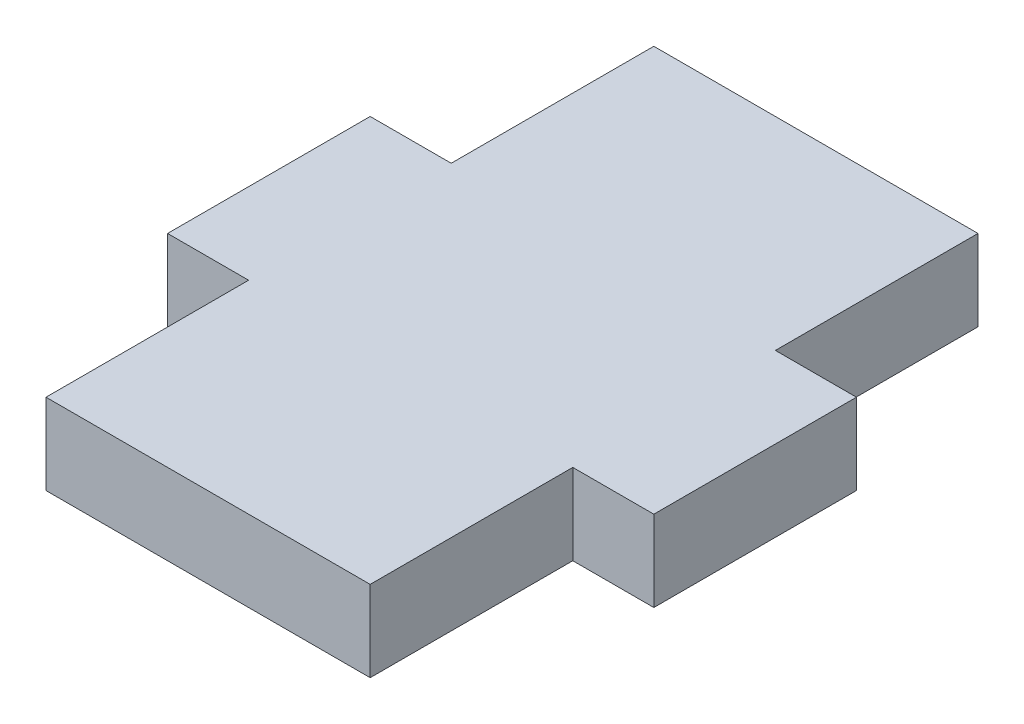
SolidWorks part; units mm, degrees
material "Stal węglowa"
ref_plane "Płaszczyzna przednia" through (0, 0, 0) normal (0, 0, 1) x (1, 0, 0)
ref_plane "Płaszczyzna górna" through (0, 0, 0) normal (0, 1, 0) x (1, 0, 0)
ref_plane "Płaszczyzna prawa" through (0, 0, 0) normal (1, 0, 0) x (0, 0, -1)
sketch "Szkic1" plane through (0, 0, 0) normal (0, 0, 1) x (1, 0, 0)
  line L0 (-8, -373.3248) -> (-8, -375.3201)
  line L1 (0, -373.3248) -> (0, -375.3201)
  line L3 (-8, -375.3201) -> (0, -375.3201)
  line L8 (-8, -373.3248) -> (-8, -360.3201)
  line L9 (-8, -360.3201) -> (-10, -360.3201)
  line L10 (-10, -360.3201) -> (-10, -375.3201)
  line L11 (-10, -375.3201) -> (2, -375.3201)
  line L12 (2, -375.3201) -> (2, -360.3201)
  line L13 (2, -360.3201) -> (0, -360.3201)
  line L14 (0, -360.3201) -> (0, -373.3248)
  line L15 (0, -373.3248) -> (-8, -373.3248)
  line L23 (0, -373.3248) -> (-8, -373.3248)
  dimension "D1" = 0
extrude "Dodanie-wyciągnięcie1" add sketch "Szkic1" against normal blind 15 contours L3 L1 L23 L0
sketch "Szkic3" plane through (-8, 0, 0) normal (-1, 0, 0) x (0, 0, 1)
  line L1 (-15, -375.3201) -> (0, -375.3201) construction
  line L2 (-15, -373.3248) -> (0, -373.3248) construction
  line L3 (-10, -375.3201) -> (-5, -375.3201)
  line L4 (-10, -375.3201) -> (-10, -373.3248)
  line L5 (-10, -373.3248) -> (-5, -373.3248)
  line L6 (-5, -375.3201) -> (-5, -373.3248)
extrude "Dodanie-wyciągnięcie2" add sketch "Szkic3" along normal blind 2
sketch "Szkic5" plane through (0, 0, 0) normal (1, 0, 0) x (0, 0, -1)
  line L1 (15, -375.3201) -> (0, -375.3201) construction
  line L2 (15, -373.3248) -> (0, -373.3248) construction
  line L3 (5, -375.3201) -> (10, -375.3201)
  line L4 (5, -375.3201) -> (5, -373.3248)
  line L5 (5, -373.3248) -> (10, -373.3248)
  line L6 (10, -375.3201) -> (10, -373.3248)
extrude "Dodanie-wyciągnięcie3" add sketch "Szkic5" along normal blind 2 contours L6 L5 L4 L3
